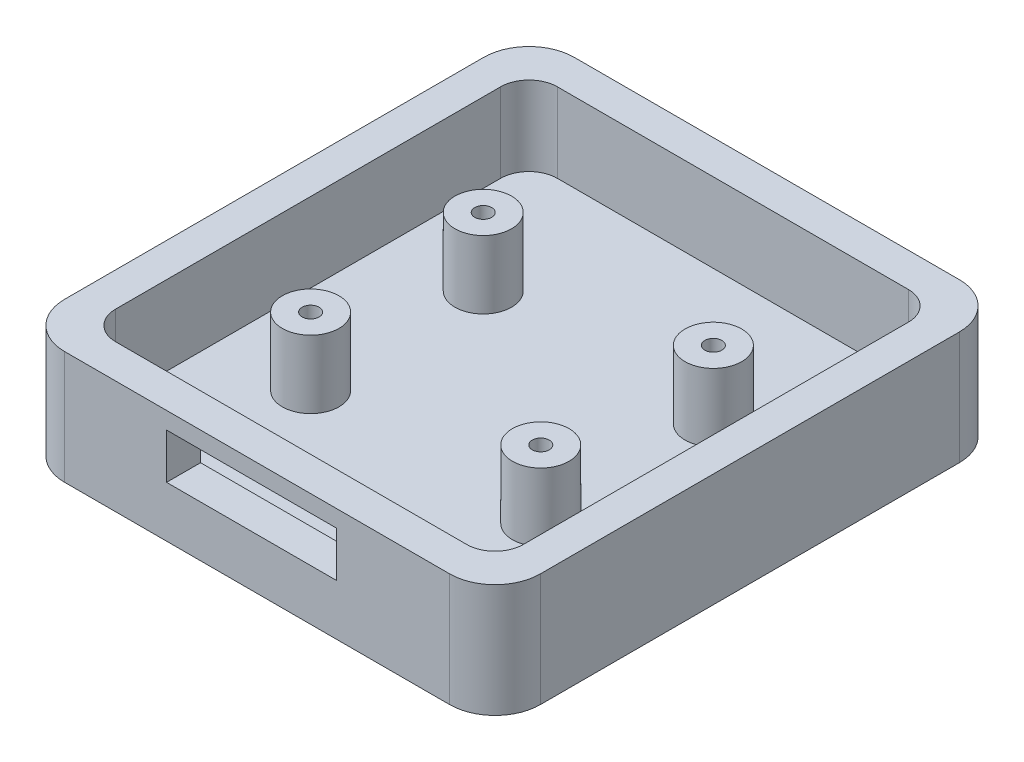
SolidWorks part; units mm, degrees
ref_plane "Front Plane" through (0, 0, 0) normal (0, 0, 1) x (1, 0, 0)
ref_plane "Top Plane" through (0, 0, 0) normal (0, 1, 0) x (1, 0, 0)
ref_plane "Right Plane" through (0, 0, 0) normal (1, 0, 0) x (0, 0, -1)
sketch "Sketch1" plane through (0, 0, 0) normal (0, 1, 0) x (1, 0, 0)
  line L1 (21, 22.5) -> (-21, 22.5)
  line L2 (21, 22.5) -> (21, -22.5)
  line L3 (21, -22.5) -> (-21, -22.5)
  line L4 (-21, 22.5) -> (-21, -22.5)
  line L5 (21, 22.5) -> (-21, -22.5) construction
  line L6 (21, -22.5) -> (-21, 22.5) construction
  line L7 (-18, 19.5) -> (18, 19.5)
  line L8 (-18, 19.5) -> (-18, -19.5)
  line L9 (-18, -19.5) -> (18, -19.5)
  line L10 (18, 19.5) -> (18, -19.5)
  line L11 (-18, 19.5) -> (18, -19.5) construction
  line L12 (-18, -19.5) -> (18, 19.5) construction
  point P0 (0, 0)
  point P6 (0, 0)
  dimension "D1" = 42
  dimension "D2" = 45
  dimension "D3" = 3
  dimension "D4" = 3
extrude "Boss-Extrude1" add sketch "Sketch1" along normal blind 10
sketch "Sketch2" plane through (0, 0, 0) normal (0, -1, 0) x (1, 0, 0)
  line L0 (18, -19.5) -> (-18, -19.5) construction
  line L1 (-18, 19.5) -> (18, 19.5)
  line L2 (-18, 19.5) -> (-18, -19.5)
  line L3 (-18, -19.5) -> (18, -19.5)
  line L4 (18, 19.5) -> (18, -19.5)
  line L5 (-18, 19.5) -> (18, -19.5) construction
  line L6 (-18, -19.5) -> (18, 19.5) construction
  line L7 (18, 19.5) -> (18, -19.5) construction
  point P0 (0, 0)
extrude "Boss-Extrude2" add sketch "Sketch2" against normal blind 3
fillet "Fillet1" radius 4 4 edges at (21, 5, 22.5) (-21, 5, 22.5) (-21, 5, -22.5) (21, 5, -22.5)
sketch "Sketch3" plane through (0, 3, 0) normal (0, 1, 0) x (1, 0, 0)
  circle A0 centre (-10.16, 7.62) radius 2.5
  circle A1 centre (10.16, 7.62) radius 2.5
  circle A2 centre (-10.16, -7.62) radius 2.5
  circle A3 centre (10.16, -7.62) radius 2.5
  point P0 (0, 0)
  dimension "D3" = 5
  dimension "D4" = 5
  dimension "D5" = 5
  dimension "D6" = 5
  dimension "D1" = 20.32
  dimension "D2" = 15.24
extrude "Boss-Extrude3" add sketch "Sketch3" along normal blind 6
sketch "Sketch4" plane through (0, 9, 0) normal (0, 1, 0) x (1, 0, 0)
  circle A4 centre (-10.16, 7.62) radius 0.75
  circle A5 centre (-10.16, -7.62) radius 0.75
  circle A6 centre (10.16, -7.62) radius 0.75
  circle A7 centre (10.16, 7.62) radius 0.75
  dimension "D1" = 1.5
  dimension "D2" = 1.5
  dimension "D3" = 1.5
  dimension "D4" = 1.5
extrude "Cut-Extrude1" cut sketch "Sketch4" against normal blind 5
sketch "Sketch5" plane through (0, 0, 19.5) normal (0, 0, -1) x (-1, 0, 0)
  line L0 (18, 10) -> (18, 3) construction
  line L1 (-7, 8.5) -> (8, 8.5)
  line L2 (-7, 8.5) -> (-7, 4.5)
  line L3 (-7, 4.5) -> (8, 4.5)
  line L4 (8, 8.5) -> (8, 4.5)
  line L5 (-7, 8.5) -> (8, 4.5) construction
  line L6 (-7, 4.5) -> (8, 8.5) construction
  line L7 (18, 10) -> (-18, 10) construction
  point P0 (0.5, 6.5)
  dimension "D1" = 15
  dimension "D2" = 10
  dimension "D3" = 4
  dimension "D4" = 1.5
extrude "Cut-Extrude2" cut sketch "Sketch5" against normal blind 15
sketch "Sketch6" plane through (-21, 0, 0) normal (-1, 0, 0) x (0, 0, 1)
  line L0 (-18.5, 2.7738) -> (18.5, 2.7738) construction
  line L1 (-18.5, 10) -> (-18.5, 0) construction
  line L2 (18.5, 0) -> (18.5, 10) construction
  text T0 "4019" font "BankGothic Md BT" height 3.5
extrude "Cut-Extrude3" cut sketch "Sketch6" against normal blind 0.2
fillet "Fillet2" radius 2.5 4 edges at (18, 6.5, 19.5) (-18, 6.5, 19.5) (-18, 6.5, -19.5) (18, 6.5, -19.5)
